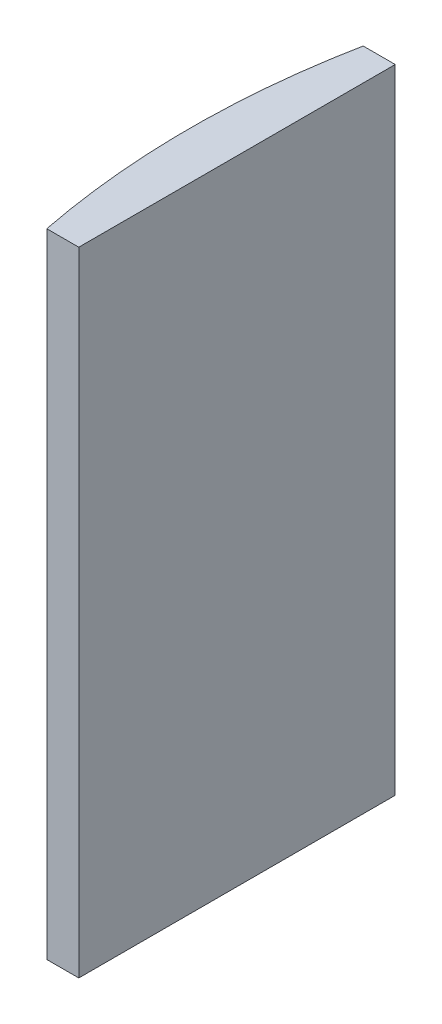
SolidWorks part; units mm, degrees
ref_plane "前视基准面" through (0, 0, 0) normal (0, 0, 1) x (1, 0, 0)
ref_plane "上视基准面" through (0, 0, 0) normal (0, 1, 0) x (1, 0, 0)
ref_plane "右视基准面" through (0, 0, 0) normal (1, 0, 0) x (0, 0, -1)
sketch "草图1" plane through (0, 0, 0) normal (0, 1, 0) x (1, 0, 0)
  line L0 (10.7432, 0) -> (-607.0701, 0) construction
  line L1 (-71.7303, 15) -> (-68.6948, 15)
  line L2 (-71.7303, -15) -> (-68.6948, -15)
  line L3 (-68.6948, 15) -> (-68.6948, -15)
  arc A0 (-71.7303, 15) -> (-71.7303, -15) centre (4.3552, 0) ccw
  point P19 (-73.1948, 0)
  point P20 (-68.6948, 0)
  dimension "D2" = 15
  dimension "D3" = 77.55
  dimension "D4" = 4.5
  dimension "D1" = 15
extrude "凸台-拉伸1" add sketch "草图1" along normal blind 60
